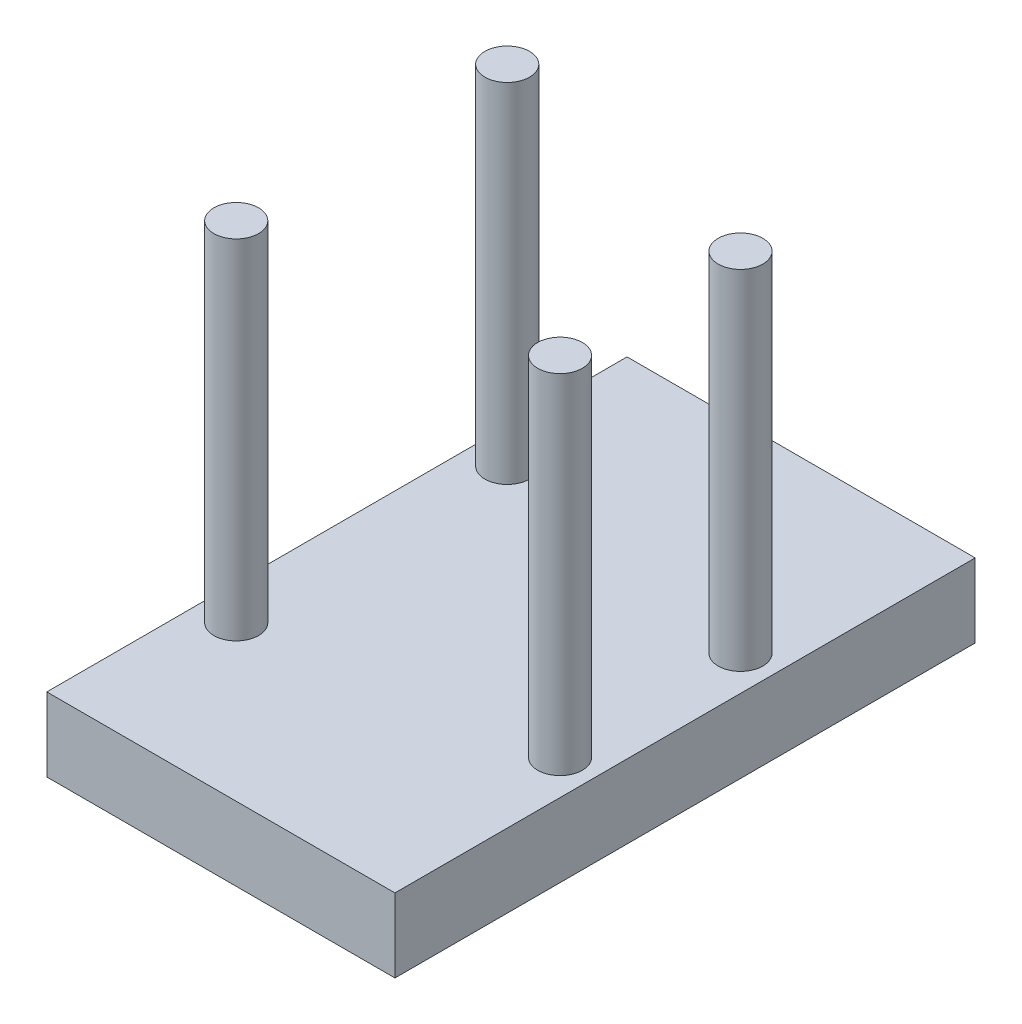
SolidWorks part; units mm, degrees
ref_plane "Front Plane" through (0, 0, 0) normal (0, 0, 1) x (1, 0, 0)
ref_plane "Top Plane" through (0, 0, 0) normal (0, 1, 0) x (1, 0, 0)
ref_plane "Right Plane" through (0, 0, 0) normal (1, 0, 0) x (0, 0, -1)
sketch "Sketch1" plane through (0, 0, 0) normal (0, 1, 0) x (1, 0, 0)
  line L1 (30, -50) -> (-30, -50)
  line L2 (30, -50) -> (30, 50)
  line L3 (30, 50) -> (-30, 50)
  line L4 (-30, -50) -> (-30, 50)
  line L5 (30, -50) -> (-30, 50) construction
  line L6 (30, 50) -> (-30, -50) construction
  point P0 (0, 0)
  dimension "D1" = 60
  dimension "D2" = 100
extrude "Boss-Extrude1" add sketch "Sketch1" along normal blind 12.7
ref_point "Center"
ref_plane "Qaurterway " through (0, 0, 25) normal (0, 0, 1) x (1, 0, 0)
ref_plane "Quarterway" through (0, 0, -25) normal (0, 0, 1) x (1, 0, 0)
ref_plane "Plane3" through (21.45, 0, 0) normal (1, 0, 0) x (0, 0, -1)
ref_plane "Plane4" through (-21.45, 0, 0) normal (1, 0, 0) x (0, 0, -1)
sketch "Sketch7" plane through (0, 12.7, 0) normal (0, 1, 0) x (1, 0, 0)
  line L0 (0, 0) -> (-24, 0)
  line L1 (-6.985, 0) -> (6.985, 0) construction
  line L2 (0, 0) -> (24, 0)
  line L3 (-24, 0) -> (-24, 23.35)
  line L4 (-24, 0) -> (-24, -23.35)
  line L5 (24, 0) -> (24, 15.55)
  line L6 (24, 0) -> (24, -15.55)
  dimension "D1" = 24
  dimension "D2" = 24
  dimension "D3" = 23.35
  dimension "D4" = 23.35
  dimension "D5" = 15.55
  dimension "D6" = 15.55
sketch "Sketch8" plane through (0, 12.7, 0) normal (0, 1, 0) x (1, 0, 0)
  circle A0 centre (-24, 23.35) radius 3.85
  circle A1 centre (-24, -23.35) radius 3.85
  circle A2 centre (24, -15.55) radius 3.85
  circle A3 centre (24, 15.55) radius 3.85
  dimension "D1" = 7.7
  dimension "D2" = 7.7
  dimension "D3" = 7.7
  dimension "D4" = 7.7
extrude "Boss-Extrude2" add sketch "Sketch8" along normal blind 60
